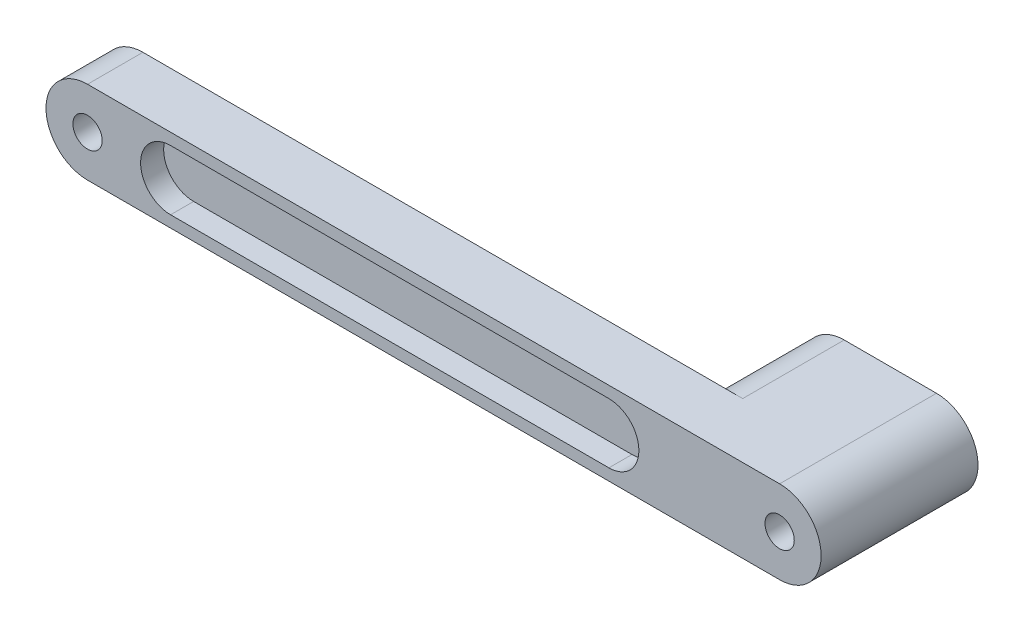
SolidWorks part; units mm, degrees
material "6061-T6 (SS)"
ref_plane "Front Plane" through (0, 0, 0) normal (0, 0, 1) x (1, 0, 0)
ref_plane "Top Plane" through (0, 0, 0) normal (0, 1, 0) x (1, 0, 0)
ref_plane "Right Plane" through (0, 0, 0) normal (1, 0, 0) x (0, 0, -1)
sketch "Sketch1" plane through (0, 0, 0) normal (0, 0, 1) x (1, 0, 0)
  line L0 (0, 0) -> (150, 0) construction
  line L1 (0, 9) -> (150, 9)
  line L2 (0, -9) -> (150, -9)
  circle A0 centre (0, 0) radius 3.175
  circle A1 centre (150, 0) radius 3.175
  arc A2 (0, 9) -> (0, -9) centre (0, 0) ccw
  arc A3 (150, -9) -> (150, 9) centre (150, 0) ccw
  point P5 (75, 0)
  dimension "D1" = 150
  dimension "D2" = 6.35
  dimension "D3" = 9
extrude "Boss-Extrude1" add sketch "Sketch1" along normal blind 12
sketch "Sketch2" plane through (0, 0, 0) normal (0, 0, -1) x (-1, 0, 0)
  line L0 (-150, 0) -> (-130, 0) construction
  line L1 (-150, 9) -> (-130, 9)
  line L2 (-150, -9) -> (-130, -9)
  arc A0 (-150, 9) -> (-150, -9) centre (-150, 0) ccw
  arc A1 (-130, -9) -> (-130, 9) centre (-130, 0) ccw
  arc A2 (-150, 9) -> (-150, -9) centre (-150, 0) ccw construction
  circle A3 centre (-150, 0) radius 3.175 construction
  circle A4 centre (-150, 0) radius 3.175
  point P4 (-140, 0)
  dimension "D1" = 20
extrude "Boss-Extrude2" add sketch "Sketch2" along normal blind 22
sketch "Sketch3" plane through (0, 0, 12) normal (0, 0, 1) x (1, 0, 0)
  line L0 (18, 0) -> (113, 0) construction
  line L1 (18, 6.5) -> (113, 6.5)
  line L2 (18, -6.5) -> (113, -6.5)
  line L3 (150, 9) -> (0, 9) construction
  arc A0 (18, 6.5) -> (18, -6.5) centre (18, 0) ccw
  arc A1 (113, -6.5) -> (113, 6.5) centre (113, 0) ccw
  circle A2 centre (150, 0) radius 3.175 construction
  circle A3 centre (0, 0) radius 3.175 construction
  point P3 (65.5, 0)
  dimension "D1" = 2.5
  dimension "D2" = 37
  dimension "D3" = 18
extrude "Cut-Extrude1" cut sketch "Sketch3" against normal blind 5
ref_plane "Plane1" through (0, 0, 6) normal (0, 0, 1) x (1, 0, 0)
mirror "Mirror1" about plane through (0, 0, 6) normal (0, 0, 1) of "Cut-Extrude1"
sketch "Sketch4" plane through (0, 0, -22) normal (0, 0, -1) x (-1, 0, 0)
  line L0 (-138, -6) -> (-130, -6)
  line L1 (-130, 6) -> (-138, 6)
  line L4 (-150, -9) -> (-130, -9)
  line L5 (-130, 9) -> (-150, 9)
  line L6 (-150, -9) -> (-130, -9)
  line L7 (-130, 9) -> (-150, 9)
  line L9 (-130, 6) -> (-150, 6) construction
  line L10 (-150, -6) -> (-130, -6) construction
  arc A1 (-130, -6) -> (-130, 6) centre (-130, 0) ccw
  arc A4 (-150, 9) -> (-150, -9) centre (-150, 0) ccw
  arc A5 (-130, -9) -> (-130, 9) centre (-130, 0) ccw
  arc A6 (-150, 9) -> (-150, -9) centre (-150, 0) ccw
  arc A7 (-130, -9) -> (-130, 9) centre (-130, 0) ccw
  arc A8 (-138, 6) -> (-138, -6) centre (-138, 0) ccw
  arc A9 (-150, 6) -> (-150, -6) centre (-150, 0) ccw construction
  dimension "D2" = 6
  dimension "D3" = 8
  dimension "D1" = 0
extrude "Cut-Extrude2" cut sketch "Sketch4" against normal blind 30 contours L1 A8 L0 A1
